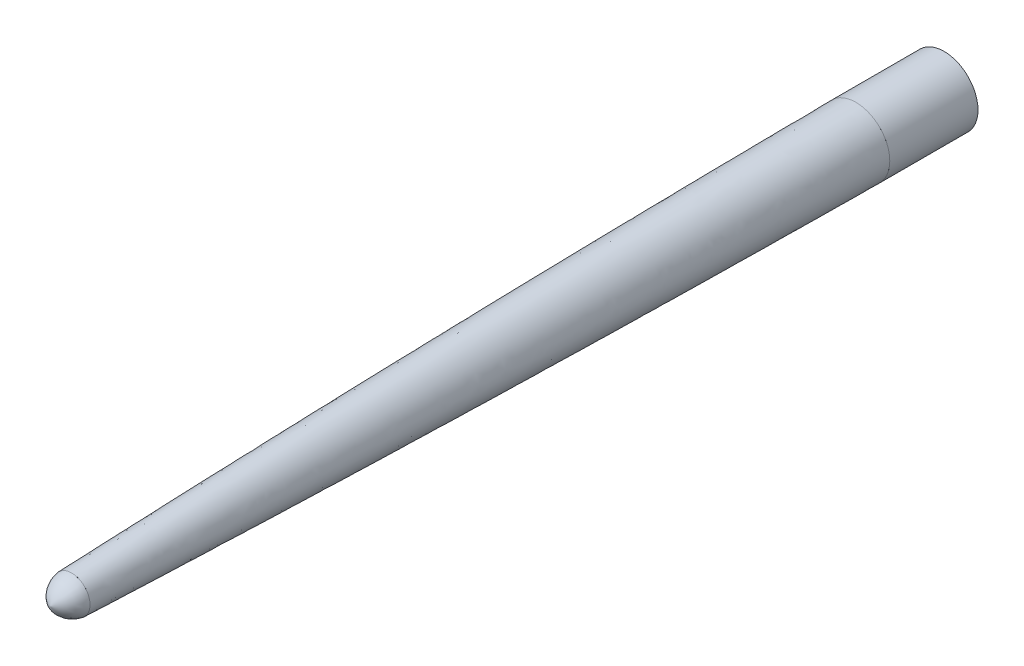
SolidWorks part; units mm, degrees
ref_plane "前基準面" through (0, 0, 0) normal (0, 0, 1) x (1, 0, 0)
ref_plane "上基準面" through (0, 0, 0) normal (0, 1, 0) x (1, 0, 0)
ref_plane "右基準面" through (0, 0, 0) normal (1, 0, 0) x (0, 0, -1)
sketch "草圖1" plane through (0, 0, 0) normal (0, 0, 1) x (1, 0, 0)
  circle A0 centre (0, 0) radius 4.8
  dimension "D1" = 9.6
extrude "填料-伸長1" add sketch "草圖1" along normal blind 12.5 contours A0
sketch "草圖2" plane through (0, 0, 12.5) normal (0, 0, 1) x (1, 0, 0)
  circle A1 centre (0, 0) radius 4.8
  dimension "D1" = 9.6
ref_plane "平面1" through (0, 0, 123.6) normal (0, 0, 1) x (1, 0, 0)
sketch "草圖3" plane through (0, 0, 123.6) normal (0, 0, 1) x (1, 0, 0)
  circle A0 centre (0, 0) radius 2.6
  dimension "D1" = 5.2
sketch "草圖4" plane through (0, 0, 0) normal (0, 1, 0) x (1, 0, 0)
  line L1 (-2.6, -123.6) -> (2.6, -123.6) construction
  line L2 (0, -12.5) -> (0, -123.6) construction
  line L3 (-4.8, -12.5) -> (4.8, -12.5) construction
  arc A0 (4.8, -12.5) -> (2.6, -123.6) centre (-2995.1975, -8.6659) cw
  arc A1 (-4.8, -12.5) -> (-2.6, -123.6) centre (2995.1975, -8.6659) ccw
  point P5 (0, 0)
  point P11 (0, 0)
  dimension "D1" = 3000
sketch "草圖5" plane through (0, 0, 0) normal (1, 0, 0) x (0, 0, -1)
  line L1 (-123.6, 2.6) -> (-123.6, -2.6) construction
  line L2 (-123.6, 0) -> (-12.5, 0) construction
  line L3 (-12.5, 4.8) -> (-12.5, -4.8) construction
  arc A0 (-123.6, 2.6) -> (-12.5, 4.8) centre (-8.6659, -2995.1975) cw
  arc A1 (-123.6, -2.6) -> (-12.5, -4.8) centre (-8.6659, 2995.1975) ccw
  point P5 (0, 0)
  point P7 (0, 0)
  point P16 (0, 0)
  point P18 (0, 0)
  point P20 (0, 0)
  point P22 (0, 0)
  dimension "D1" = 3000
surface "曲面-疊層拉伸1"
surface "曲面-平面1"
surface "曲面-平面2"
sketch "草圖6" plane through (0, 0, 0) normal (0, 1, 0) x (1, 0, 0)
  line L2 (0, -123.6) -> (0, -124.677) construction
  line L4 (2.6, -123.6) -> (-2.6, -123.6) construction
  line L5 (0, -123.6) -> (-2.6, -123.6)
  line L7 (0, -123.6) -> (0, -126.6)
  arc A5 (-2.6, -123.6) -> (0, -126.6) centre (1.0205, -123.0889) ccw
revolve "旋轉3" add sketch "草圖6" angle 360 about L2
